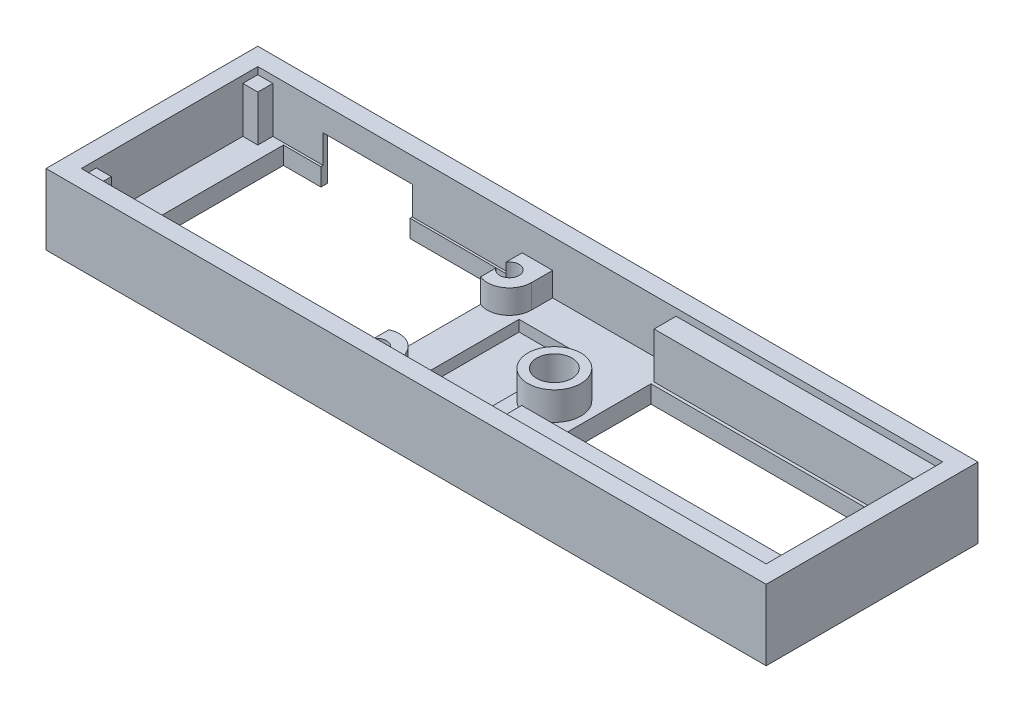
SolidWorks part; units mm, degrees
ref_plane "Front Plane" through (0, 0, 0) normal (0, 0, 1) x (1, 0, 0)
ref_plane "Top Plane" through (0, 0, 0) normal (0, 1, 0) x (1, 0, 0)
ref_plane "Right Plane" through (0, 0, 0) normal (1, 0, 0) x (0, 0, -1)
sketch "Sketch2" plane through (0, 0, 0) normal (0, 1, 0) x (1, 0, 0)
  line L0 (40.8, -12) -> (-40.8, -12)
  line L1 (38.8, -10) -> (-38.8, -10)
  line L2 (38.8, -10) -> (38.8, 10)
  line L3 (38.8, 10) -> (-38.8, 10)
  line L4 (-38.8, -10) -> (-38.8, 10)
  line L5 (38.8, -10) -> (-38.8, 10) construction
  line L6 (38.8, 10) -> (-38.8, -10) construction
  line L11 (-40.8, -12) -> (-40.8, 12)
  line L12 (40.8, 12) -> (-40.8, 12)
  line L13 (40.8, -12) -> (40.8, 12)
  point P0 (0, 0)
  point P6 (0, 0)
  dimension "D2" = 77.6
  dimension "D3" = 20
  dimension "D1" = 2
extrude "Boss-Extrude1" add sketch "Sketch2" along normal blind 8
sketch "Sketch3" plane through (0, 0, 0) normal (0, 1, 0) x (1, 0, 0)
  line L0 (38.8, 10) -> (-38.8, 10) construction
  line L1 (38.8, 10) -> (-38.8, 10)
  line L2 (-38.8, -10) -> (38.8, -10) construction
  line L3 (38.8, -10) -> (38.8, 10) construction
  line L4 (-38.8, 10) -> (-38.8, -10) construction
  line L5 (-38.8, -10) -> (38.8, -10)
  line L6 (38.8, -10) -> (38.8, 10)
  line L7 (-38.8, 10) -> (-38.8, -10)
extrude "Boss-Extrude2" add sketch "Sketch3" along normal blind 2
sketch "Sketch4" plane through (0, 8, 0) normal (0, 1, 0) x (1, 0, 0)
  line L0 (-38.8, 10) -> (-38.8, -10) construction
  line L1 (-35.65, -9.75) -> (-8.85, -9.75)
  line L2 (-35.65, -9.75) -> (-35.65, 9.75)
  line L3 (-35.65, 9.75) -> (-8.85, 9.75)
  line L4 (-8.85, -9.75) -> (-8.85, 9.75)
  line L5 (-35.65, -9.75) -> (-8.85, 9.75) construction
  line L6 (-35.65, 9.75) -> (-8.85, -9.75) construction
  line L7 (38.8, -10) -> (38.8, 10) construction
  line L8 (38.8, 7.15) -> (8.6, 7.15)
  line L9 (38.8, 7.15) -> (38.8, -7.15)
  line L10 (38.8, -7.15) -> (8.6, -7.15)
  line L11 (8.6, 7.15) -> (8.6, -7.15)
  line L12 (38.8, 7.15) -> (8.6, -7.15) construction
  line L13 (38.8, -7.15) -> (8.6, 7.15) construction
  circle A0 centre (4.8, 0) radius 2
  point P0 (-22.25, 0)
  point P5 (23.7, 0)
  point P6 (0, 0)
  point P14 (0, 0)
  dimension "D6" = 4
  dimension "D1" = 26.8
  dimension "D2" = 19.5
  dimension "D3" = 3.15
  dimension "D4" = 30.2
  dimension "D5" = 14.3
  dimension "D7" = 34
extrude "Cut-Extrude1" cut sketch "Sketch4" against normal through all
sketch "Sketch6" plane through (0, 2, 0) normal (0, 1, 0) x (-1, 0, 0)
  line L20 (-8.6, -7.15) -> (-8.6, 7.15) construction
  line L21 (-38.8, 10) -> (-8.6, 10)
  line L22 (-38.8, 10) -> (-38.8, 7.5)
  line L23 (-38.8, 7.5) -> (-8.6, 7.5)
  line L24 (-8.6, 10) -> (-8.6, 7.5)
  line L25 (-38.8, -10) -> (-8.6, -10)
  line L26 (-38.8, -10) -> (-38.8, -7.5)
  line L27 (-38.8, -7.5) -> (-8.6, -7.5)
  line L28 (-8.6, -10) -> (-8.6, -7.5)
  line L30 (38.8, 10) -> (37.1, 10)
  line L31 (38.8, 10) -> (38.8, 8.3)
  line L32 (38.8, 8.3) -> (37.1, 8.3)
  line L33 (37.1, 10) -> (37.1, 8.3)
  line L34 (38.8, -10) -> (37.1, -10)
  line L35 (38.8, -10) -> (38.8, -8.3)
  line L36 (38.8, -8.3) -> (37.1, -8.3)
  line L37 (37.1, -10) -> (37.1, -8.3)
  dimension "D1" = 2.5
  dimension "D2" = 1.7
extrude "Boss-Extrude5" add sketch "Sketch6" along normal offset from surface (5.2 mm away) 0.8 up to face at (0, 8, 0)
sketch "Sketch11" plane through (0, 2, 0) normal (0, 1, 0) x (1, 0, 0)
  circle A0 centre (4.8, 0) radius 3
  circle A1 centre (4.8, 0) radius 2 construction
  circle A2 centre (4.8, 0) radius 2
  dimension "D1" = 1
extrude "Boss-Extrude6" add sketch "Sketch11" along normal offset from surface (3.2 mm away) 2.8 up to face at (0, 8, 0)
sketch "Sketch8" plane through (0, 2, 0) normal (0, 1, 0) x (1, 0, 0)
  line L2 (-38.8, 10) -> (-38.8, -10) construction
  line L3 (38.8, 10) -> (-38.8, 10) construction
  line L4 (-8.85, -9.75) -> (-8.85, 9.75) construction
  line L5 (-8.85, -9.75) -> (-8.85, -5.0875)
  line L6 (-5.4, 10) -> (-8.85, 10)
  line L7 (-38.8, -10) -> (38.8, -10) construction
  line L9 (-8.85, -9.75) -> (-8.85, -10)
  line L10 (-8.85, 9.75) -> (-8.85, 10)
  line L11 (-8.85, 5.2875) -> (-8.85, 9.75)
  line L12 (-5.4, -7.4) -> (-5.4, -10)
  line L13 (-5.4, -10) -> (-8.85, -10)
  line L14 (-5.4, 7.6) -> (-5.4, 10)
  arc A0 (-8.85, 5.2875) -> (-5.4, 7.6) centre (-7.9, 7.6) ccw
  arc A1 (-5.4, -7.4) -> (-8.85, -5.0875) centre (-7.9, -7.4) ccw
  point P19 (0, 0)
  point P20 (0, 0)
  point P21 (-5.4226, 10)
  dimension "D2" = 5
  dimension "D1" = 15
  dimension "D3" = 30.9
  dimension "D4" = 2.4
extrude "Boss-Extrude7" add sketch "Sketch8" along normal offset from surface (2.7 mm away) 2.5 up to face at (23.7, 7.2, -8.75)
sketch "Sketch13" plane through (0, 4.7, 0) normal (0, 1, 0) x (1, 0, 0)
  circle A0 centre (-7.9, 7.6) radius 1.1
  circle A1 centre (-7.9, -7.4) radius 1.1
  dimension "D1" = 2.2
extrude "Cut-Extrude2" cut sketch "Sketch13" against normal offset from surface (4 mm away) 0.7 up to face at (-22.25, 0, 0)
sketch "Sketch15" plane through (0, 0, -12) normal (0, 0, -1) x (-1, 0, 0)
  line L1 (21.3, 5.2) -> (31.4, 5.2)
  line L2 (21.3, 5.2) -> (21.3, 0)
  line L3 (21.3, 0) -> (31.4, 0)
  line L4 (31.4, 5.2) -> (31.4, 0)
  line L7 (38.8, 7.2) -> (38.8, 2) construction
  line L8 (-40.8, 0) -> (40.8, 0) construction
  line L9 (-40.8, 8) -> (40.8, 8) construction
  point P8 (0, 0)
  point P9 (0, 0)
  dimension "D1" = 7.4
  dimension "D2" = 17.5
  dimension "D3" = 2.8
extrude "Cut-Extrude3" cut sketch "Sketch15" against normal up to next
chamfer "Chamfer1" distance 1.5 angle 45 3 edges at (-31.4, 2.6, -12) (-26.35, 5.2, -12) (-21.3, 2.6, -12)
sketch "Sketch16" plane through (0, 2, 0) normal (0, 1, 0) x (1, 0, 0)
  line L0 (38.8, -10) -> (38.8, 10) construction
  line L1 (-5.2, 6) -> (1.8, 6)
  line L2 (-5.2, 6) -> (-5.2, -6)
  line L3 (-5.2, -6) -> (1.8, -6)
  line L4 (1.8, 6) -> (1.8, -6)
  line L5 (-5.2, 6) -> (1.8, -6) construction
  line L6 (-5.2, -6) -> (1.8, 6) construction
  circle A0 centre (4.8, 0) radius 3 construction
  point P0 (-1.7, 0)
  point P5 (0, 0)
  dimension "D1" = 12
  dimension "D2" = 44
extrude "Cut-Extrude4" cut sketch "Sketch16" against normal offset from surface (1.25 mm away) 0.75 up to face at (-17.65, 0, -4.6071)
